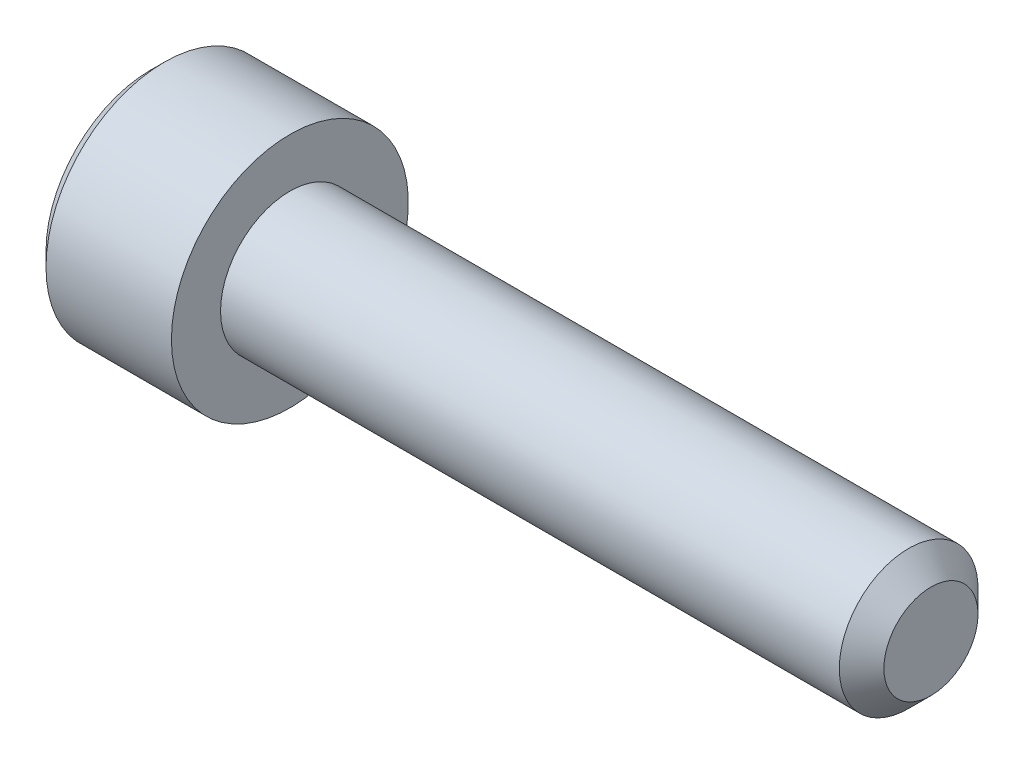
SolidWorks part; units mm, degrees
material "AISI Type 316L stainless steel"
ref_plane "Front Plane" through (0, 0, 0) normal (0, 0, 1) x (1, 0, 0)
ref_plane "Top Plane" through (0, 0, 0) normal (0, 1, 0) x (1, 0, 0)
ref_plane "Right Plane" through (0, 0, 0) normal (1, 0, 0) x (0, 0, -1)
sketch "Sketch1" plane through (0, 0, 0) normal (0, 0, 1) x (1, 0, 0)
  line L0 (-88.7055, 0) -> (96.9812, 0) construction
  line L1 (0, 0) -> (0, 4.25)
  line L2 (0, 4.25) -> (5, 4.25)
  line L4 (28, 0) -> (28, 2.488)
  line L5 (28, 2.488) -> (5, 2.488)
  line L6 (5, 2.488) -> (5, 4.25)
  line L7 (0, 0) -> (28, 0)
  dimension "D1" = 23
  dimension "D2" = 2.488
  dimension "D3" = 4.25
  dimension "D4" = 5
revolve "Revolve1" add sketch "Sketch1" angle 360 about L0
chamfer "Chamfer1" distance 0.8 angle 45 1 edges at (28, 0, 2.488)
chamfer "Chamfer2" distance 0.5 angle 45 1 edges at (0, 0, 4.25)
sketch "Sketch3" plane through (0, 0, 0) normal (1, 0, 0) x (0, 0, -1)
  line L1 (-2.3094, 0) -> (-1.1547, -2)
  line L2 (-1.1547, -2) -> (1.1547, -2)
  line L3 (1.1547, -2) -> (2.3094, 0)
  line L4 (2.3094, 0) -> (1.1547, 2)
  line L5 (1.1547, 2) -> (-1.1547, 2)
  line L6 (-1.1547, 2) -> (-2.3094, 0)
  circle A0 centre (0, 0) radius 2 construction
  dimension "D1" = 4
extrude "Cut-Extrude1" cut sketch "Sketch3" along normal blind 2.5
chamfer "Chamfer3" distance 0.4 angle 45 6 edges at (0, 2, 0) (0, 1, 1.7321) (0, -1, 1.7321) (0, -2, 0) (0, -1, -1.7321) (0, 1, -1.7321)
sketch "Sketch5" plane through (28, 0, 0) normal (1, 0, 0) x (0, 0, -1)
  circle A0 centre (0, 0) radius 2.488
  dimension "D1" = 4.976
curve "Helix/Spiral1" pitch 0.8 height 55 turns 68.75
sketch "Sketch8" plane through (0, 0, 0) normal (0, 1, 0) x (1, 0, 0)
  line L0 (28, 2.488) -> (28, 1.8816) construction
  line L1 (28.1, 2.0549) -> (28.5251, 2.7912)
  line L2 (28.5251, 2.7912) -> (27.4749, 2.7912)
  line L3 (27.4749, 2.7912) -> (27.9, 2.0549)
  line L4 (28, -1.688) -> (28, 1.688) construction
  circle A0 centre (28, 2.488) radius 0.3032 construction
  arc A1 (28.1, 2.0549) -> (27.9, 2.0549) centre (28, 2.1126) cw
  dimension "D2" = 0.1155
  dimension "D1" = 0.6064
equation "\"length\"= 23"
equation "\"D1@Sketch1\"=\"length\""
